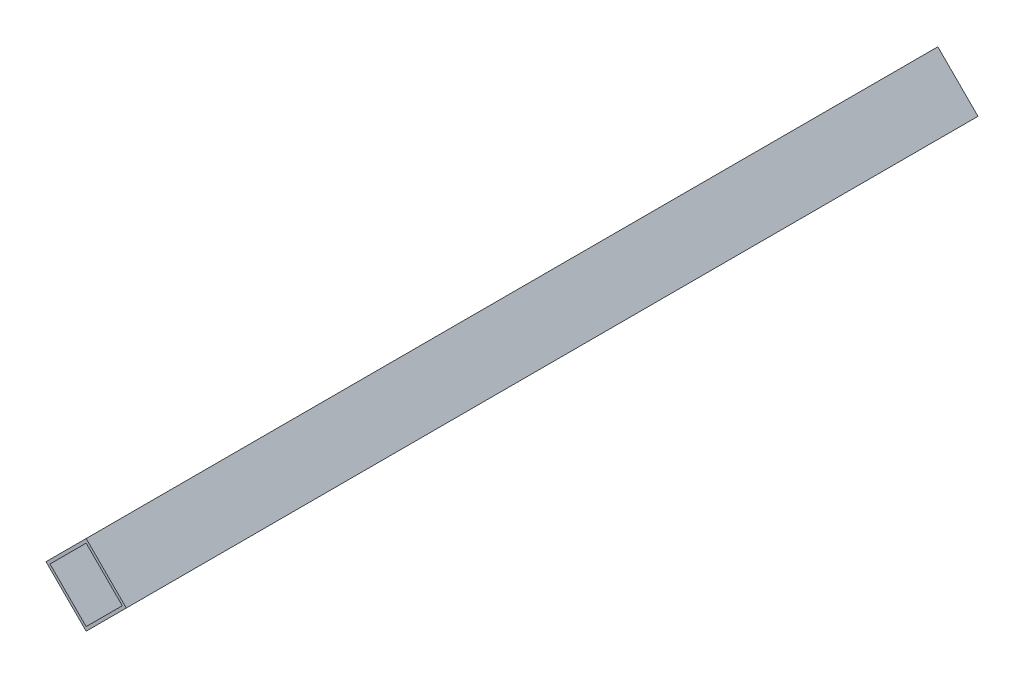
SolidWorks part; units mm, degrees
material "1060 合金"
ref_plane "前视基准面" through (0, 0, 0) normal (0, 0, 1) x (1, 0, 0)
ref_plane "上视基准面" through (0, 0, 0) normal (0, 1, 0) x (1, 0, 0)
ref_plane "右视基准面" through (0, 0, 0) normal (1, 0, 0) x (0, 0, -1)
other "Configuration Table"
sketch "草图1" plane through (0, 0, 0) normal (0, 0, 1) x (1, 0, 0)
  line L1 (14.1421, 0) -> (0, 14.1421)
  line L2 (0, 14.1421) -> (-14.1421, 0)
  line L3 (-14.1421, 0) -> (0, -14.1421)
  line L4 (0, -14.1421) -> (14.1421, 0)
  line L5 (12.7279, 0) -> (0, 12.7279)
  line L6 (0, 12.7279) -> (-12.7279, 0)
  line L7 (-12.7279, 0) -> (0, -12.7279)
  line L8 (0, -12.7279) -> (12.7279, 0)
  circle A0 centre (0, 0) radius 10 construction
  circle A1 centre (0, 0) radius 9 construction
  dimension "D1" = 20
  dimension "D2" = 18
extrude "凸台-拉伸1" add sketch "草图1" along normal blind 300
sketch "草图2" plane through (7.0711, -7.0711, 0) normal (0.7071, -0.7071, 0) x (0, 0, -1)
  line L3 (-300, -10) -> (-300, 10) construction
  line L4 (-300, -10) -> (0, -10) construction
  circle A0 centre (-290, 0) radius 1
  circle A1 centre (-220, 0) radius 1
  circle A2 centre (-150, 0) radius 1
  circle A3 centre (-80, 0) radius 1
  circle A4 centre (-10, 0) radius 1
  dimension "D1" = 2
  dimension "D2" = 10
  dimension "D3" = 10
  dimension "D5" = 70
  dimension "D4" = 5
extrude "切除-拉伸1" cut sketch "草图2" against normal through all
